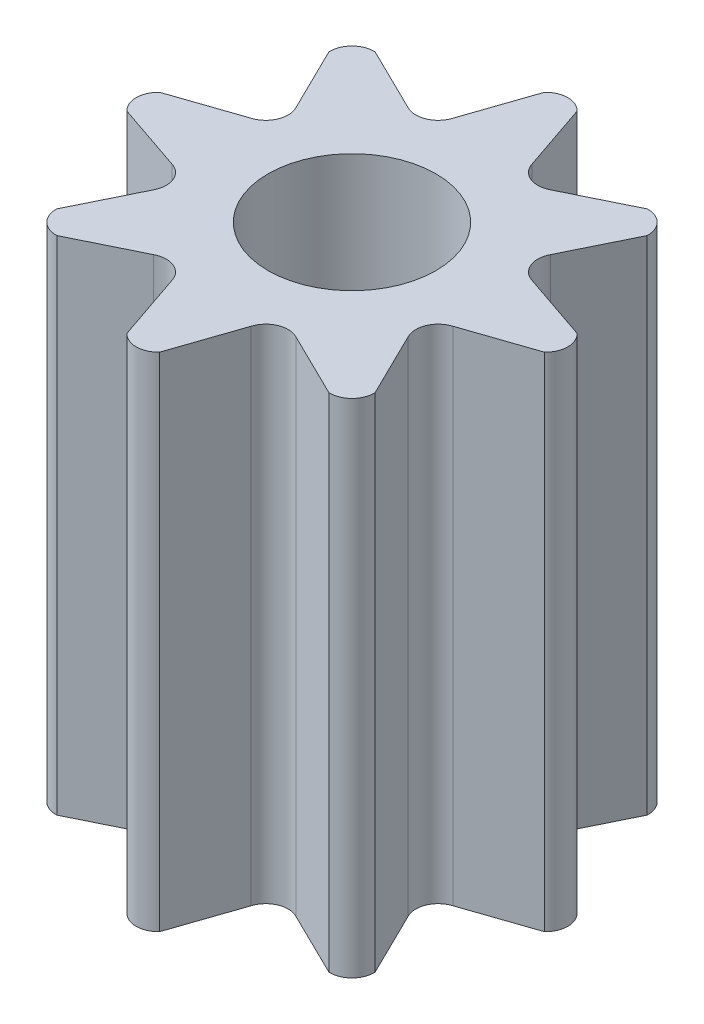
SolidWorks part; units mm, degrees
material "1060 Alloy"
ref_plane "Front Plane" through (0, 0, 0) normal (0, 0, 1) x (1, 0, 0)
ref_plane "Top Plane" through (0, 0, 0) normal (0, 1, 0) x (1, 0, 0)
ref_plane "Right Plane" through (0, 0, 0) normal (1, 0, 0) x (0, 0, -1)
sketch "Sketch1" plane through (0, 0, 0) normal (0, 1, 0) x (1, 0, 0)
  line L0 (2.3, 0) -> (1.6263, 1.6263) construction
  line L1 (0, 2.3) -> (-1.6263, 1.6263) construction
  line L2 (-1.6263, 1.6263) -> (-2.3, 0) construction
  line L3 (-2.3, 0) -> (-1.6263, -1.6263) construction
  line L4 (-1.6263, -1.6263) -> (0, -2.3) construction
  line L5 (0, -2.3) -> (1.6263, -1.6263) construction
  line L6 (1.6263, -1.6263) -> (2.3, 0) construction
  line L7 (1.6263, 1.6263) -> (0, 2.3) construction
  line L8 (0, 2.3) -> (0, -2.3) construction
  line L9 (-0.8132, 1.9632) -> (-0.4305, 1.0393) construction
  line L10 (-0.4305, 1.0393) -> (0, 2.3) construction
  line L11 (0.8132, 1.9632) -> (0.4305, 1.0393) construction
  line L12 (0.4305, 1.0393) -> (0, 2.3) construction
  line L13 (-0.4305, 1.0393) -> (0.4305, 1.0393) construction
  line L14 (-0.4973, 1.2005) -> (-0.3554, 1.2593) construction
  line L15 (0.3554, 1.2593) -> (0.4973, 1.2005) construction
  line L16 (-0.1464, 1.8714) -> (0.1464, 1.8714) construction
  line L17 (-0.1464, 1.8714) -> (-0.3554, 1.2593)
  line L18 (0.1464, 1.8714) -> (0.3554, 1.2593)
  line L19 (1.2198, 1.4267) -> (0.6392, 1.1417)
  line L20 (1.4267, 1.2198) -> (1.1417, 0.6392)
  line L21 (1.8714, 0.1464) -> (1.2593, 0.3554)
  line L22 (1.8714, -0.1464) -> (1.2593, -0.3554)
  line L23 (1.4267, -1.2198) -> (1.1417, -0.6392)
  line L24 (1.2198, -1.4267) -> (0.6392, -1.1417)
  line L25 (0.1464, -1.8714) -> (0.3554, -1.2593)
  line L26 (-0.1464, -1.8714) -> (-0.3554, -1.2593)
  line L27 (-1.2198, -1.4267) -> (-0.6392, -1.1417)
  line L28 (-1.4267, -1.2198) -> (-1.1417, -0.6392)
  line L29 (-1.8714, -0.1464) -> (-1.2593, -0.3554)
  line L30 (-1.8714, 0.1464) -> (-1.2593, 0.3554)
  line L31 (-1.4267, 1.2198) -> (-1.1417, 0.6392)
  line L32 (-1.2198, 1.4267) -> (-0.6392, 1.1417)
  circle A0 centre (0, 0) radius 2.3 construction
  circle A1 centre (0, 0) radius 0.7525
  arc A2 (-0.1464, 1.8714) -> (0.1464, 1.8714) centre (0, 1.7351) cw
  arc A3 (-0.3554, 1.2593) -> (-0.4698, 1.1341) centre (-0.5463, 1.3189) cw
  arc A4 (0.3554, 1.2593) -> (0.4698, 1.1341) centre (0.5463, 1.3189) ccw
  arc A5 (0.6392, 1.1417) -> (0.4698, 1.1341) centre (0.5463, 1.3189) cw
  arc A6 (1.2198, 1.4267) -> (1.4267, 1.2198) centre (1.2269, 1.2269) cw
  arc A7 (1.1417, 0.6392) -> (1.1341, 0.4698) centre (1.3189, 0.5463) ccw
  arc A8 (1.2593, 0.3554) -> (1.1341, 0.4698) centre (1.3189, 0.5463) cw
  arc A9 (1.8714, 0.1464) -> (1.8714, -0.1464) centre (1.7351, 0) cw
  arc A10 (1.2593, -0.3554) -> (1.1341, -0.4698) centre (1.3189, -0.5463) ccw
  arc A11 (1.1417, -0.6392) -> (1.1341, -0.4698) centre (1.3189, -0.5463) cw
  arc A12 (1.4267, -1.2198) -> (1.2198, -1.4267) centre (1.2269, -1.2269) cw
  arc A13 (0.6392, -1.1417) -> (0.4698, -1.1341) centre (0.5463, -1.3189) ccw
  arc A14 (0.3554, -1.2593) -> (0.4698, -1.1341) centre (0.5463, -1.3189) cw
  arc A15 (0.1464, -1.8714) -> (-0.1464, -1.8714) centre (0, -1.7351) cw
  arc A16 (-0.3554, -1.2593) -> (-0.4698, -1.1341) centre (-0.5463, -1.3189) ccw
  arc A17 (-0.6392, -1.1417) -> (-0.4698, -1.1341) centre (-0.5463, -1.3189) cw
  arc A18 (-1.2198, -1.4267) -> (-1.4267, -1.2198) centre (-1.2269, -1.2269) cw
  arc A19 (-1.1417, -0.6392) -> (-1.1341, -0.4698) centre (-1.3189, -0.5463) ccw
  arc A20 (-1.2593, -0.3554) -> (-1.1341, -0.4698) centre (-1.3189, -0.5463) cw
  arc A21 (-1.8714, -0.1464) -> (-1.8714, 0.1464) centre (-1.7351, 0) cw
  arc A22 (-1.2593, 0.3554) -> (-1.1341, 0.4698) centre (-1.3189, 0.5463) ccw
  arc A23 (-1.1417, 0.6392) -> (-1.1341, 0.4698) centre (-1.3189, 0.5463) cw
  arc A24 (-1.4267, 1.2198) -> (-1.2198, 1.4267) centre (-1.2269, 1.2269) cw
  arc A25 (-0.6392, 1.1417) -> (-0.4698, 1.1341) centre (-0.5463, 1.3189) ccw
  point P92 (0, 0)
  dimension "D2" = 1.505
  dimension "D4" = 0.2
  dimension "D5" = 0.2
  dimension "D6" = 0.2
  dimension "D1" = 4.6
  dimension "D3" = 1
  dimension "D7" = 0.22
  dimension "D8" = 0.22
  dimension "D9" = 0.34
  dimension "D10" = 8
extrude "Boss-Extrude1" add sketch "Sketch1" along normal blind 4.5
sketch "Axis" plane through (0, 0, 0) normal (1, 0, 0) x (0, 0, -1)
  line L0 (0, 0) -> (0, 4.5) construction
  line L1 (0.1464, 4.5) -> (-0.1464, 4.5) construction
